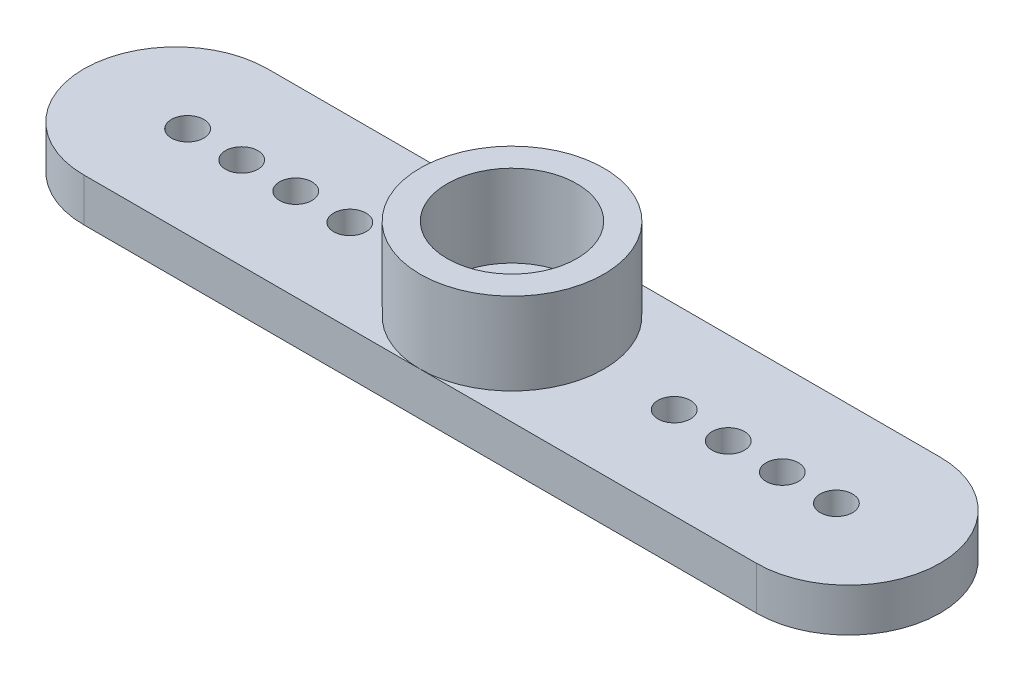
SolidWorks part; units mm, degrees
ref_plane "Спереди" through (0, 0, 0) normal (0, 0, 1) x (1, 0, 0)
ref_plane "Сверху" through (0, 0, 0) normal (0, 1, 0) x (1, 0, 0)
ref_plane "Справа" through (0, 0, 0) normal (1, 0, 0) x (0, 0, -1)
sketch "Эскиз1" plane through (0, 0, 0) normal (0, 1, 0) x (1, 0, 0)
  line L0 (0, 0) -> (31.1, 0) construction
  line L1 (0, 4.25) -> (31.1, 4.25)
  line L2 (0, -4.25) -> (31.1, -4.25)
  arc A0 (0, 4.25) -> (0, -4.25) centre (0, 0) ccw
  arc A1 (31.1, -4.25) -> (31.1, 4.25) centre (31.1, 0) ccw
  circle A2 centre (8.05, 0) radius 0.75
  circle A3 centre (23.05, 0) radius 0.75
  circle A4 centre (25.55, 0) radius 0.75
  circle A5 centre (28.05, 0) radius 0.75
  circle A6 centre (30.55, 0) radius 0.75
  circle A7 centre (5.55, 0) radius 0.75
  circle A8 centre (3.05, 0) radius 0.75
  circle A9 centre (0.55, 0) radius 0.75
  point P2 (15.55, 0)
  point P8 (-4.25, 0)
  point P9 (35.35, 0)
  dimension "D1" = 4.25
  dimension "D3" = 7.5
  dimension "D4" = 1.5
  dimension "D7" = 1.5
  dimension "D2" = 39.6
  dimension "D6" = 7.5
  dimension "D5" = 4
  dimension "D8" = 4
extrude "Бобышка-Вытянуть1" add sketch "Эскиз1" along normal blind 2
sketch "Эскиз2" plane through (0, 2, 0) normal (0, 1, 0) x (1, 0, 0)
  line L0 (-4.25, 0) -> (35.35, 0) construction
  circle A0 centre (15.55, 0) radius 4.25
  arc A1 (0, 4.25) -> (0, -4.25) centre (0, 0) ccw construction
  arc A2 (31.1, -4.25) -> (31.1, 4.25) centre (31.1, 0) ccw construction
  dimension "D1" = 8.5
extrude "Бобышка-Вытянуть2" add sketch "Эскиз2" along normal blind 3.8
sketch "Эскиз3" plane through (0, 5.8, 0) normal (0, 1, 0) x (1, 0, 0)
  circle A0 centre (15.55, 0) radius 3
  dimension "D1" = 6
extrude "Вырез-Вытянуть1" cut sketch "Эскиз3" against normal blind 3.8
